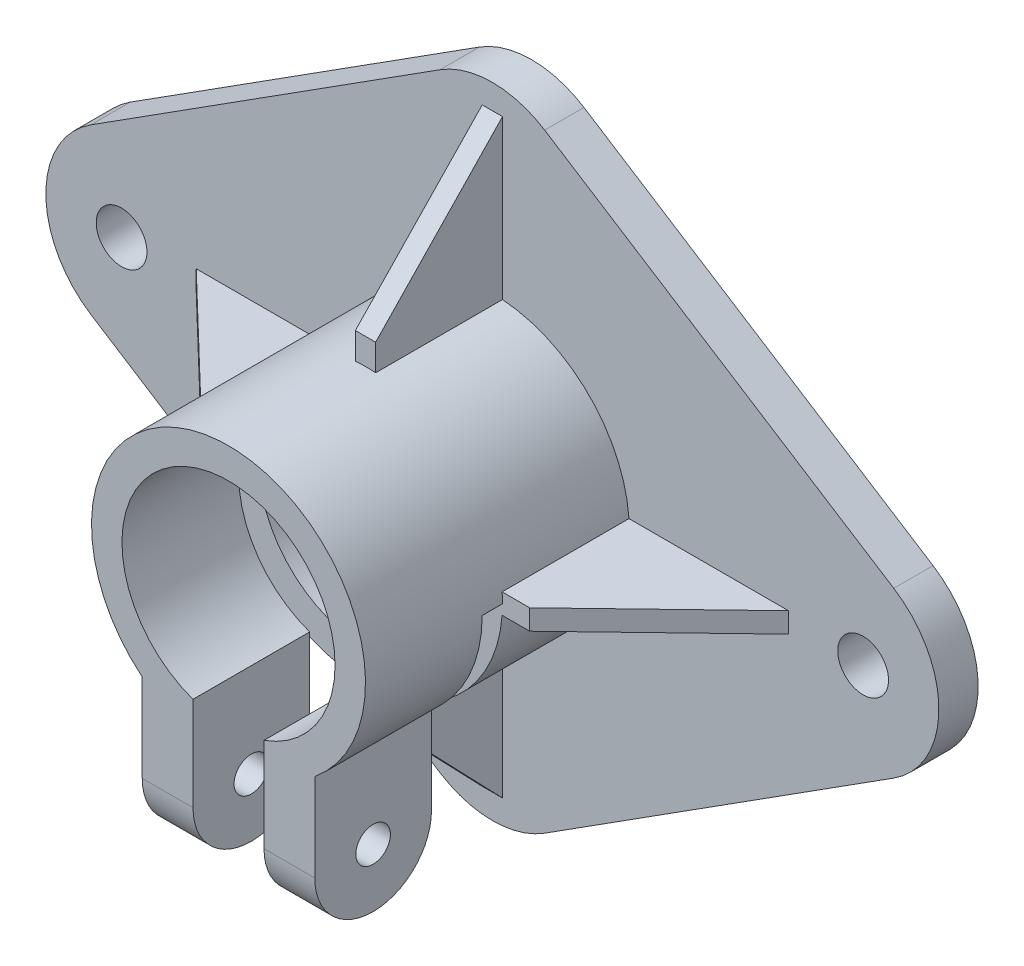
SolidWorks part; units mm, degrees
material "ABS"
ref_plane "Front Plane" through (0, 0, 0) normal (0, 0, 1) x (1, 0, 0)
ref_plane "Top Plane" through (0, 0, 0) normal (0, 1, 0) x (1, 0, 0)
ref_plane "Right Plane" through (0, 0, 0) normal (1, 0, 0) x (0, 0, -1)
sketch "Sketch1" plane through (0, 0, 0) normal (0, 0, 1) x (1, 0, 0)
  line L0 (-41.494, 0) -> (0, 26.4163) construction
  line L1 (-41.494, 0) -> (0, -26.4163) construction
  line L2 (-41.494, 0) -> (41.494, 0) construction
  line L3 (0, 26.4163) -> (41.494, 0) construction
  line L4 (41.494, 0) -> (0, -26.4163) construction
  line L5 (0, 26.4163) -> (0, -26.4163) construction
  line L6 (-31.3972, 6.4279) -> (-4.0922, 23.8111)
  line L7 (4.0922, 23.8111) -> (31.3972, 6.4279)
  line L8 (31.3972, -6.4279) -> (4.0922, -23.8111)
  line L9 (-4.0922, -23.8111) -> (-31.3972, -6.4279)
  line L10 (-29, 0) -> (29, 0) construction
  circle A0 centre (0, 0) radius 8.3344
  arc A1 (31.3972, 6.4279) -> (31.3972, -6.4279) centre (27.305, 0) cw
  arc A2 (4.0922, -23.8111) -> (-4.0922, -23.8111) centre (0, -17.3831) cw
  arc A3 (-4.0922, 23.8111) -> (4.0922, 23.8111) centre (0, 17.3831) cw
  arc A4 (-31.3972, 6.4279) -> (-31.3972, -6.4279) centre (-27.305, 0) ccw
  point P5 (0, 0)
  point P8 (0, 0)
  point P21 (-29, 0)
  point P22 (29, 0)
  point P28 (0, 0)
  point P29 (0, 25.0031)
  point P30 (0, -25.0031)
  point P32 (-34.925, 0)
  point P33 (34.925, 0)
  dimension "D1" = 16.6687
  dimension "D2" = 69.85
  dimension "D3" = 50.0062
  dimension "D4" = 7.62
  dimension "D5" = 58
extrude "Boss-Extrude1" add sketch "Sketch1" along normal blind 3.0734
hole_wizard "#6 Clearance Hole1" positions "Sketch2" profile "Sketch3" hole size "#6" standard "ANSI Inch" end condition through all
sketch "Sketch2" plane through (0, 0, 3.0734) normal (0, 0, 1) x (1, 0, 0)
  point P0 (-29, 0)
  point P3 (29, 0)
sketch "Sketch3" plane through (-29, 0, 3.0734) normal (1, 0, 0) x (0, -1, 0)
  line L0 (0, 0) -> (0, 3.0734)
  line L1 (0, 3.0734) -> (1.9844, 3.0734)
  line L2 (1.9844, 3.0734) -> (1.9844, 0)
  line L5 (1.9844, 0) -> (0, 0)
  line L11 (0, -6.35) -> (0, 107.95) construction
  dimension "Thru Hole Dia." = 3.9688
  dimension "Thru Hole Depth" = 3.0734
sketch "Sketch4" plane through (0, 0, 3.0734) normal (0, 0, 1) x (1, 0, 0)
  circle A0 centre (0, 0) radius 8.3344
  circle A1 centre (0, 0) radius 10.7156
  dimension "D1" = 2.3813
extrude "Boss-Extrude2" add sketch "Sketch4" along normal blind 20.6375
sketch "Sketch6" plane through (0, 0, 0) normal (0, 1, 0) x (1, 0, 0)
  line L0 (-10.7156, -3.0734) -> (-10.7156, -23.7109) construction
  line L1 (-10.7156, -12.9953) -> (10.7156, -12.9953)
  line L2 (-10.7156, -12.9953) -> (-10.7156, -14.5828)
  line L3 (-10.7156, -14.5828) -> (-2.7781, -14.5828)
  line L4 (10.7156, -12.9953) -> (10.7156, -14.5828)
  line L5 (10.7156, -23.7109) -> (10.7156, -3.0734) construction
  line L6 (4.0922, -3.0734) -> (31.3972, -3.0734) construction
  line L7 (-10.7156, -23.7109) -> (10.7156, -23.7109) construction
  line L9 (-2.7781, -14.5828) -> (-2.7781, -23.7109)
  line L10 (-2.7781, -23.7109) -> (2.7781, -23.7109)
  line L11 (2.7781, -14.5828) -> (2.7781, -23.7109)
  line L13 (2.7781, -14.5828) -> (10.7156, -14.5828)
  dimension "D1" = 1.5875
  dimension "D2" = 9.9219
  dimension "D3" = 5.5562
  dimension "D4" = 7.9375
extrude "Cut-Extrude1" cut sketch "Sketch6" against normal through all
ref_plane "Plane1" through (0, -7.8577, 0) normal (0, 1, 0) x (1, 0, 0)
sketch "Sketch7" plane through (0, -7.8577, 0) normal (0, 1, 0) x (1, 0, 0)
  line L0 (-2.7781, -14.5828) -> (-8.3344, -14.5828) construction
  line L1 (-2.7781, -23.7109) -> (-6.7469, -23.7109)
  line L2 (-2.7781, -23.7109) -> (-2.7781, -14.5828)
  line L3 (-2.7781, -14.5828) -> (-6.7469, -14.5828)
  line L4 (-6.7469, -23.7109) -> (-6.7469, -14.5828)
  line L5 (10.7156, -14.5828) -> (2.7781, -14.5828) construction
  line L6 (2.7781, -23.7109) -> (6.7469, -23.7109)
  line L7 (2.7781, -23.7109) -> (2.7781, -14.5828)
  line L8 (2.7781, -14.5828) -> (6.7469, -14.5828)
  line L9 (6.7469, -23.7109) -> (6.7469, -14.5828)
  dimension "D1" = 3.9688
  dimension "D2" = 3.9688
extrude "Boss-Extrude3" add sketch "Sketch7" against normal blind 11.9062
sketch "Sketch8" plane through (-6.7469, 0, 0) normal (-1, 0, 0) x (0, 0, 1)
  line L0 (23.7109, -19.764) -> (23.7109, -8.3249) construction
  line L1 (14.5828, -19.764) -> (14.5828, -8.3249) construction
  line L2 (14.5828, -19.764) -> (23.7109, -19.764) construction
  line L3 (23.7109, -15.1999) -> (23.7109, -21.0502)
  line L4 (23.7109, -21.0502) -> (14.5828, -21.0502)
  line L5 (14.5828, -21.0502) -> (14.5828, -15.1999)
  arc A0 (23.7109, -15.1999) -> (14.5828, -15.1999) centre (19.1468, -15.1999) cw
  point P11 (19.1468, -19.764)
  point P14 (19.1468, -19.764)
extrude "Cut-Extrude2" cut sketch "Sketch8" against normal through all
hole_wizard "#2 Clearance Hole1" positions "Sketch9" profile "Sketch10" hole size "#2" standard "ANSI Inch" end condition through all
sketch "Sketch9" plane through (-6.7469, 0, 0) normal (-1, 0, 0) x (0, 0, 1)
  arc A0 (14.5828, -15.1999) -> (23.7109, -15.1999) centre (19.1468, -15.1999) ccw construction
  point P0 (19.1468, -15.1999)
sketch "Sketch10" plane through (-6.7469, -15.1999, 19.1468) normal (0, 1, 0) x (0, 0, 1)
  line L0 (0, 0) -> (0, 41.6719)
  line L1 (0, 41.6719) -> (1.3525, 41.6719)
  line L2 (1.3525, 41.6719) -> (1.3525, 0)
  line L5 (1.3525, 0) -> (0, 0)
  line L11 (0, -6.35) -> (0, 107.95) construction
  dimension "Thru Hole Dia." = 2.7051
  dimension "Thru Hole Depth" = 41.6719
sketch "Sketch11" plane through (0, 0, 0) normal (0, 1, 0) x (1, 0, 0)
  line L0 (-10.4616, -12.9953) -> (-12.8429, -12.9953)
  line L2 (-23.1616, -3.0734) -> (-10.4616, -3.0734)
  line L3 (-10.4616, -3.0734) -> (-10.4616, -12.9953)
  line L4 (0, -23.7109) -> (0, -3.0734) construction
  line L6 (-12.8429, -12.9953) -> (-23.1616, -3.0734)
  line L7 (-8.3344, -23.7109) -> (8.3344, -23.7109) construction
  line L8 (-4.0922, -3.0734) -> (4.0922, -3.0734) construction
  line L9 (23.1616, -3.0734) -> (10.4616, -3.0734)
  line L10 (10.4616, -3.0734) -> (10.4616, -12.9953)
  line L11 (12.8429, -12.9953) -> (23.1616, -3.0734)
  line L12 (10.4616, -12.9953) -> (12.8429, -12.9953)
  dimension "D2" = 9.9219
  dimension "D4" = 12.7
  dimension "D5" = 2.3813
  dimension "D7" = 0.254
extrude "Boss-Extrude7" add sketch "Sketch11" along normal mid plane 1.5875
sketch "Sketch13" plane through (0, 0, 0) normal (1, 0, 0) x (0, 0, -1)
  line L0 (-12.9953, 10.3775) -> (-12.9953, 12.7588)
  line L1 (55, 0) -> (-55, 0) construction
  line L2 (-3.0734, 23.0775) -> (-3.0734, 10.3775)
  line L3 (-3.0734, 10.3775) -> (-12.9953, 10.3775)
  line L4 (-43.7991, 0) -> (-3.0734, 0) construction
  line L5 (-3.0734, 6.4279) -> (-3.0734, 23.8111) construction
  line L6 (-12.9953, 12.7588) -> (-3.0734, 23.0775)
  line L9 (-3.0734, -23.0775) -> (-3.0734, -10.3775)
  line L10 (-3.0734, -10.3775) -> (-12.9953, -10.3775)
  line L11 (-12.9953, -12.7588) -> (-3.0734, -23.0775)
  line L12 (-12.9953, -10.3775) -> (-12.9953, -12.7588)
  dimension "D1" = 10.3775
  dimension "D2" = 9.9219
  dimension "D4" = 12.7
  dimension "D5" = 2.3813
extrude "Boss-Extrude8" add sketch "Sketch13" along normal mid plane 1.5875 contours L11 L9 L10 L12 | L6 L2 L3 L0
